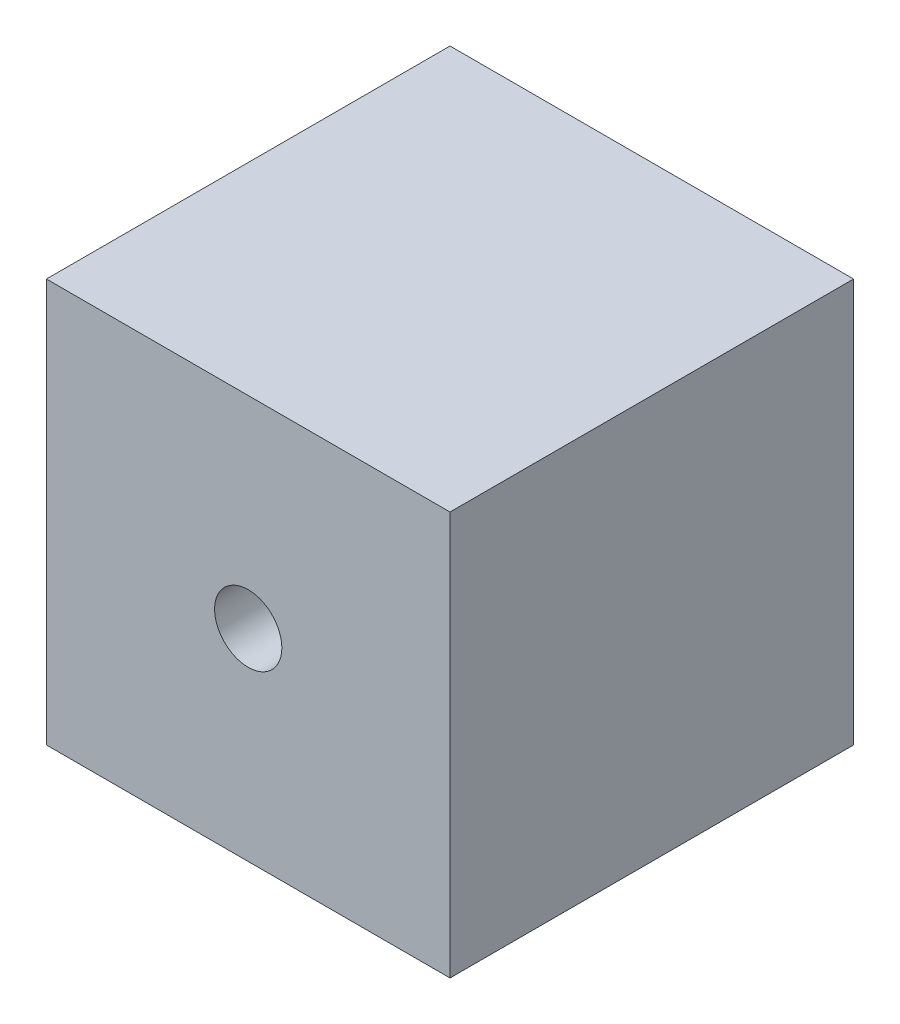
SolidWorks part; units mm, degrees
ref_plane "Front Plane" through (0, 0, 0) normal (0, 0, 1) x (1, 0, 0)
ref_plane "Top Plane" through (0, 0, 0) normal (0, 1, 0) x (1, 0, 0)
ref_plane "Right Plane" through (0, 0, 0) normal (1, 0, 0) x (0, 0, -1)
sketch "Sketch2" plane through (0, 0, 0) normal (1, 0, 0) x (0, 0, -1)
  line L0 (0, 0) -> (30, 0)
  line L1 (30, 0) -> (30, 30)
  line L2 (30, 30) -> (0, 30)
  line L3 (0, 30) -> (0, 0)
  dimension "D1" = 30
  dimension "D2" = 30
extrude "Boss-Extrude1" add sketch "Sketch2" along normal mid plane 30
sketch "Sketch3" plane through (0, 0, 0) normal (0, 0, 1) x (1, 0, 0)
  line L0 (15, 0) -> (-15, 0) construction
  circle A0 centre (0, 15) radius 2.5
  dimension "D1" = 5
  dimension "D2" = 15
extrude "Cut-Extrude1" cut sketch "Sketch3" against normal mid plane 10
